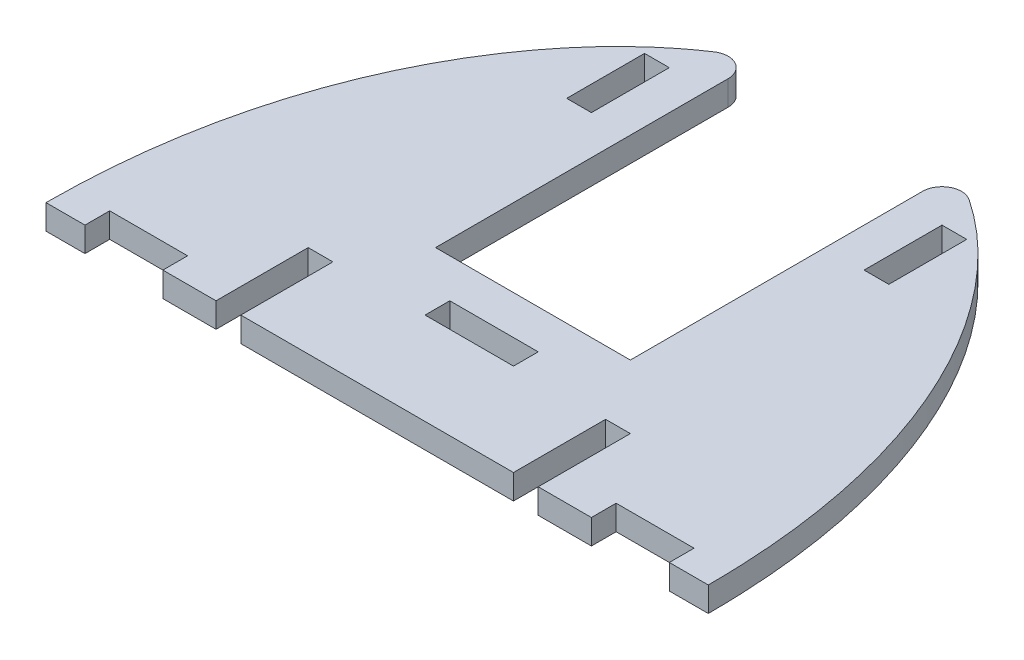
SolidWorks part; units mm, degrees
ref_plane "Front Plane" through (0, 0, 0) normal (0, 0, 1) x (1, 0, 0)
ref_plane "Top Plane" through (0, 0, 0) normal (0, 1, 0) x (1, 0, 0)
ref_plane "Right Plane" through (0, 0, 0) normal (1, 0, 0) x (0, 0, -1)
sketch "Sketch1" plane through (0, 0, 0) normal (0, 1, 0) x (1, 0, 0)
  line L0 (0, 0) -> (85, 0)
  line L1 (42.5, 0) -> (42.5, 65)
  line L2 (55.7256, 65) -> (29.1244, 65) construction
  line L3 (85, -31.5953) -> (85, 31.6135) construction
  line L4 (0, 31.3344) -> (0, -31.4206) construction
  spline S0 degree 3 poles (0, 0) (0, 36) (22.3987, 65.1749) (62.2975, 65.3077) (85, 36) (85, 0) knots 0 0 0 0 0.452811 0.552811 1 1 1 1
  dimension "D3" = 120
  dimension "D4" = 120
  dimension "D5" = 120
  dimension "D1" = 85
  dimension "D2" = 65
extrude "Boss-Extrude1" add sketch "Sketch1" along normal blind 3.175 contours S0 L0 L1 | S0 L1 L0
sketch "Sketch3" plane through (0, 3.175, 0) normal (0, 1, 0) x (1, 0, 0)
  line L0 (21.825, 0) -> (21.825, 11.825)
  line L1 (0, 0) -> (85, 0) construction
  line L2 (21.825, 11.825) -> (21.825, 0) construction
  line L3 (21.825, 11.825) -> (25, 11.825)
  line L4 (25, 11.825) -> (25, 0)
  line L5 (25, 11.825) -> (25, 0) construction
  line L6 (25, 0) -> (21.825, 0)
  line L7 (63.175, 11.825) -> (63.175, 0) construction
  line L8 (63.175, 0) -> (60, 0)
  line L9 (63.175, 0) -> (63.175, 11.825)
  line L10 (63.175, 11.825) -> (60, 11.825)
  line L11 (60, 0) -> (60, 11.825)
  line L12 (36.725, 15) -> (48.275, 15) construction
  line L13 (36.825, 15) -> (48.175, 15)
  line L14 (36.825, 15) -> (36.825, 11.825)
  line L15 (36.825, 11.825) -> (48.175, 11.825)
  line L16 (48.175, 15) -> (48.175, 11.825)
  line L17 (36.725, 11.825) -> (48.275, 11.825) construction
  line L18 (25, 55) -> (25, 44.5) construction
  line L19 (30, 20) -> (55, 20)
  line L20 (30, 20) -> (30, 69.4887)
  line L21 (30, 69.4887) -> (55, 69.4887)
  line L22 (60, 55) -> (60, 44.5) construction
  line L24 (21.825, 55) -> (21.825, 44.5) construction
  line L25 (21.825, 45) -> (25, 45)
  line L26 (21.825, 45) -> (21.825, 55)
  line L27 (21.825, 55) -> (25, 55)
  line L28 (25, 45) -> (25, 55)
  line L30 (63.175, 55) -> (60, 55)
  line L31 (63.175, 55) -> (63.175, 45)
  line L32 (63.175, 45) -> (60, 45)
  line L33 (60, 55) -> (60, 45)
  line L35 (55, 20) -> (55, 69.4887)
  line L36 (25, 11.825) -> (21.825, 11.825) construction
  line L37 (5, 0) -> (15, 0)
  line L38 (5, 0) -> (5, 3.175)
  line L39 (5, 3.175) -> (15, 3.175)
  line L40 (15, 0) -> (15, 3.175)
  line L41 (70, 0) -> (80, 0)
  line L42 (70, 0) -> (70, 3.175)
  line L43 (70, 3.175) -> (80, 3.175)
  line L44 (80, 0) -> (80, 3.175)
  line L45 (63.175, 11.825) -> (60, 11.825) construction
  point P46 (23.4125, 45)
  dimension "D1" = 15
  dimension "D2" = 15
  dimension "D3" = 5
  dimension "D4" = 5
  dimension "D5" = 10
  dimension "D6" = 5
  dimension "D7" = 3.175
  dimension "D8" = 5
  dimension "D9" = 5
  dimension "D10" = 10
  dimension "D11" = 3.175
extrude "Cut-Extrude2" cut sketch "Sketch3" against normal through all
fillet "Fillet1" radius 2.5 2 edges at (30, 1.5875, -61.8827) (55, 1.5875, -61.8554)
